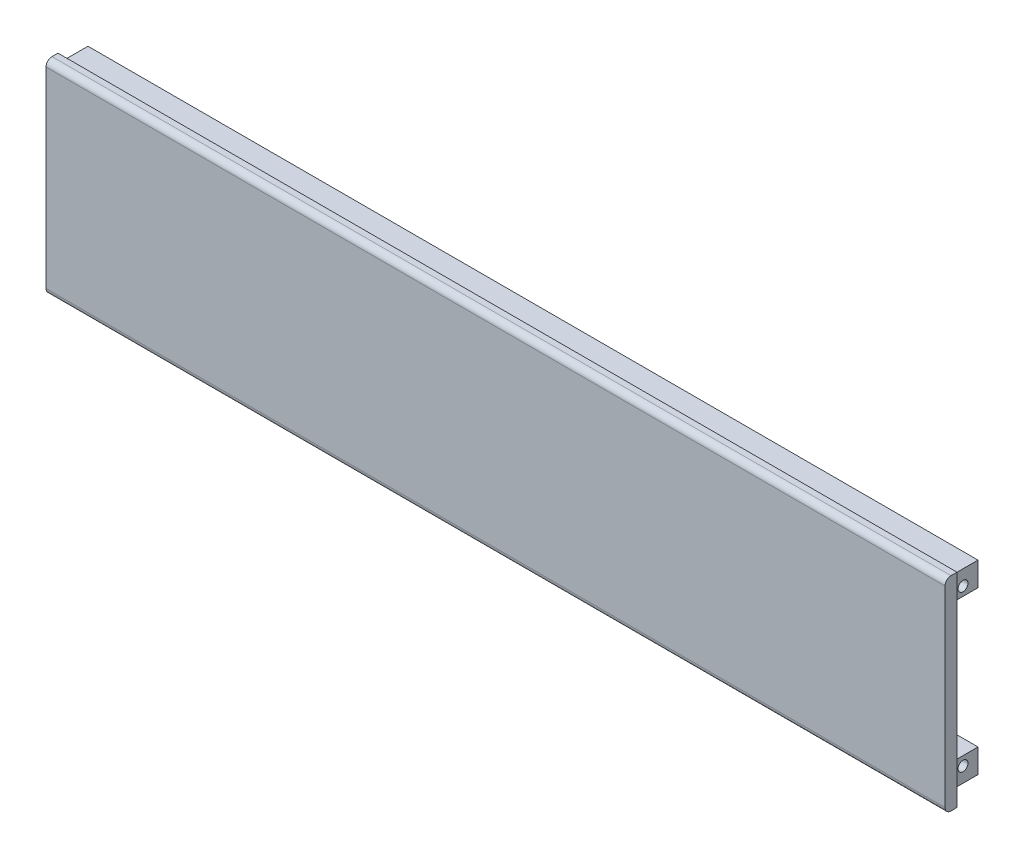
SolidWorks part; units mm, degrees
ref_plane "前基準面" through (0, 0, 0) normal (0, 0, 1) x (1, 0, 0)
ref_plane "上基準面" through (0, 0, 0) normal (0, 1, 0) x (1, 0, 0)
ref_plane "右基準面" through (0, 0, 0) normal (1, 0, 0) x (0, 0, -1)
sketch "草圖1" plane through (0, 0, 0) normal (1, 0, 0) x (0, 0, -1)
  line L1 (-2, -34) -> (2, -34)
  line L2 (-2, -34) -> (-2, 34)
  line L3 (-2, 34) -> (2, 34)
  line L4 (2, -34) -> (2, 34)
  line L5 (-2, -34) -> (2, 34) construction
  line L6 (-2, 34) -> (2, -34) construction
  point P0 (0, 0)
  dimension "D1" = 4
  dimension "D2" = 68
extrude "填料-伸長1" add sketch "草圖1" along normal blind 300
fillet "圓角1" radius 2 2 edges at (150, -34, 2) (150, 34, 2)
sketch "草圖2" plane through (0, 0, -2) normal (0, 0, -1) x (-1, 0, 0)
  line L0 (-300, -34) -> (-300, 34) construction
  line L1 (-300, 31) -> (0, 31)
  line L2 (-300, 31) -> (-300, 23)
  line L3 (-300, 23) -> (0, 23)
  line L4 (0, 31) -> (0, 23)
  line L5 (0, -34) -> (0, 34) construction
  line L6 (-300, 34) -> (0, 34) construction
  line L7 (-300, -23) -> (0, -23)
  line L8 (-300, -23) -> (-300, -31)
  line L9 (-300, -31) -> (0, -31)
  line L10 (0, -23) -> (0, -31)
  line L11 (-300, -34) -> (0, -34) construction
  dimension "D1" = 3
  dimension "D2" = 3
  dimension "D3" = 8
  dimension "D4" = 8
extrude "填料-伸長2" add sketch "草圖2" along normal blind 10
hole_wizard "M4  螺絲攻的螺孔鑽1" positions "草圖4" profile "草圖3" hole size "M4" standard "ISO" end condition through all
sketch "草圖4" plane through (300, 0, 0) normal (1, 0, 0) x (0, 0, -1)
  line L0 (12, 31) -> (12, 23) construction
  line L1 (12, 31) -> (2, 31) construction
  line L2 (12, -23) -> (12, -31) construction
  line L4 (12, -31) -> (2, -31) construction
  point P0 (7, 26)
  point P2 (7, -26)
  dimension "D1" = 5
  dimension "D2" = 5
  dimension "D3" = 5
  dimension "D4" = 5
sketch "草圖3" plane through (300, 26, -7) normal (0, 1, 0) x (0, 0, -1)
  line L0 (0, 0) -> (0, 300)
  line L1 (0, 300) -> (1.65, 300)
  line L2 (1.65, 300) -> (1.65, 0)
  line L5 (1.65, 0) -> (0, 0)
  line L11 (0, -6.35) -> (0, 107.95) construction
  dimension "貫穿孔直徑" = 3.3
  dimension "貫穿孔深度" = 300
sketch "草圖5" plane through (0, 31, 0) normal (0, 1, 0) x (1, 0, 0)
  line L0 (0, 12) -> (300, 12) construction
  line L1 (300, 2) -> (297, 2)
  line L2 (300, 2) -> (300, 12)
  line L3 (300, 12) -> (297, 12)
  line L4 (297, 2) -> (297, 12)
  dimension "D1" = 3
extrude "除料-伸長1" cut sketch "草圖5" against normal blind 62
